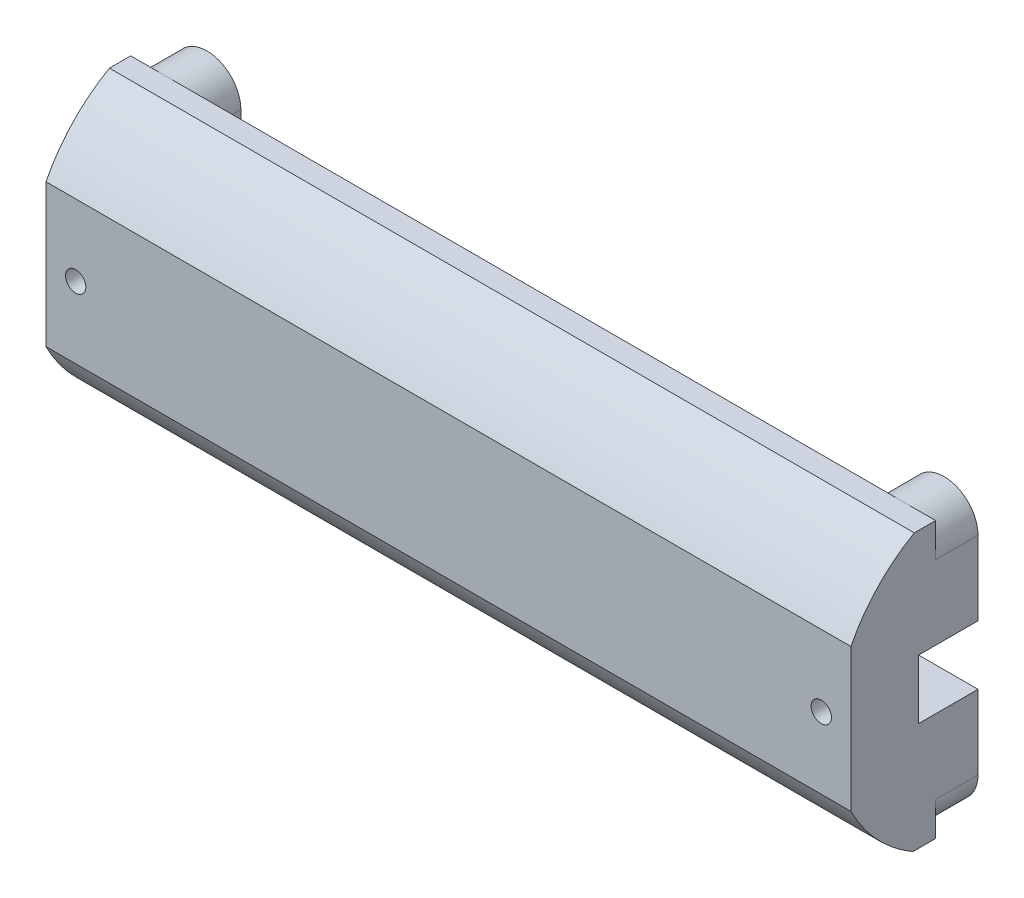
SolidWorks part; units mm, degrees
ref_plane "Front Plane" through (0, 0, 0) normal (0, 0, 1) x (1, 0, 0)
ref_plane "Top Plane" through (0, 0, 0) normal (0, 1, 0) x (1, 0, 0)
ref_plane "Right Plane" through (0, 0, 0) normal (1, 0, 0) x (0, 0, -1)
sketch "Sketch1" plane through (0, 0, 0) normal (0, 0, 1) x (1, 0, 0)
  circle A5 centre (-43.5, -12.25) radius 4
  circle A6 centre (-43.5, -12.25) radius 4
  circle A8 centre (-43.5, 12.25) radius 4
  circle A9 centre (-43.5, 12.25) radius 4
  circle A11 centre (43.5, -12.25) radius 4
  circle A12 centre (43.5, -12.25) radius 4
  circle A14 centre (43.5, 12.25) radius 4
  circle A15 centre (43.5, 12.25) radius 4
  circle A17 centre (-43.5, -12.25) radius 1.5
  circle A18 centre (-43.5, -12.25) radius 1.5
  circle A20 centre (-43.5, 12.25) radius 1.5
  circle A21 centre (-43.5, 12.25) radius 1.5
  circle A23 centre (43.5, -12.25) radius 1.5
  circle A24 centre (43.5, -12.25) radius 1.5
  circle A26 centre (43.5, 12.25) radius 1.5
  circle A27 centre (43.5, 12.25) radius 1.5
  dimension "D1" = 2.5
  dimension "D2" = 2.5
  dimension "D3" = 2.5
  dimension "D4" = 2.5
  dimension "D5" = 0
  dimension "D6" = 0
  dimension "D7" = 0
  dimension "D8" = 0
extrude "Boss-Extrude1" add sketch "Sketch1" along normal blind 5
sketch "Sketch2" plane through (0, 0, 5) normal (0, 0, 1) x (1, 0, 0)
  line L0 (-43.5, 12.25) -> (-43.5, 16.25)
  line L1 (-43.5, 16.25) -> (-47.5, 16.25)
  line L2 (43.5, -12.25) -> (47.5, -12.25)
  line L3 (47.5, -12.25) -> (47.5, -16.25)
  line L5 (-47.5, 16.25) -> (47.5, 16.25)
  line L6 (-47.5, 16.25) -> (-47.5, -16.25)
  line L7 (-47.5, -16.25) -> (47.5, -16.25)
  line L8 (47.5, 16.25) -> (47.5, -16.25)
  circle A2 centre (43.5, 12.25) radius 4
  circle A3 centre (43.5, 12.25) radius 4
  circle A4 centre (43.5, 12.25) radius 4
  circle A5 centre (-43.5, 12.25) radius 4
  circle A6 centre (-43.5, 12.25) radius 4
  circle A9 centre (43.5, -12.25) radius 4
  circle A10 centre (43.5, -12.25) radius 4
  dimension "D1" = 0
  dimension "D2" = 0
  dimension "D3" = 0
  dimension "D4" = 0
extrude "Boss-Extrude2" add sketch "Sketch2" along normal blind 10
sketch "Sketch3" plane through (0, 0, 5) normal (0, 0, -1) x (-1, 0, 0)
  line L0 (0, 16.25) -> (0, -16.25)
  line L1 (43.5, 16.25) -> (-43.5, 16.25) construction
  line L2 (43.5, -16.25) -> (-43.5, -16.25) construction
  line L3 (0, 0) -> (0, 7.1)
  line L4 (0, 7.1) -> (22.5, 7.1)
  line L5 (0, 0) -> (-6.8637, 0)
  line L6 (-22.5, -7.1) -> (22.5, -7.1)
  line L8 (-22.5, -7.1) -> (22.5, -7.1)
  line L9 (-22.5, -7.1) -> (-22.5, 7.1)
  line L10 (-22.5, 7.1) -> (22.5, 7.1)
  line L11 (22.5, -7.1) -> (22.5, 7.1)
  point P13 (0, -7.1)
extrude "Cut-Extrude1" cut sketch "Sketch3" against normal blind 9
sketch "Sketch4" plane through (0, 0, 5) normal (0, 0, -1) x (-1, 0, 0)
  line L2 (-22.5, 7.1) -> (-27.5, 7.1)
  line L3 (22.5, -7.1) -> (27.5, -7.1)
  line L5 (27.5, -7.1) -> (-27.5, -7.1)
  line L6 (27.5, -7.1) -> (27.5, 7.1)
  line L7 (27.5, 7.1) -> (-27.5, 7.1)
  line L8 (-27.5, -7.1) -> (-27.5, 7.1)
extrude "Cut-Extrude2" cut sketch "Sketch4" against normal blind 4 contours L8 L5 L2 M16 | M13 M16 M15 M14 | L6 L7 L3 M14
sketch "Sketch5" plane through (0, 0, 9) normal (0, 0, -1) x (-1, 0, 0)
  circle A2 centre (-24.8, -0.2) radius 1.4
  circle A3 centre (-24.8, -0.2) radius 1.4
  circle A5 centre (24.8, -0.2) radius 1.6
  circle A6 centre (24.8, -0.2) radius 1.6
  dimension "D1" = 0.1
  dimension "D2" = 0.1
extrude "Cut-Extrude3" cut sketch "Sketch5" against normal blind 5
sketch "Sketch6" plane through (0, 0, 5) normal (0, 0, -1) x (-1, 0, 0)
  line L4 (-47.5, 12.25) -> (-47.5, -12.25)
  line L5 (47.5, -12.25) -> (47.5, 12.25)
  line L6 (-39.5, 12.25) -> (-39.5, -12.25)
  line L7 (39.5, 12.25) -> (39.5, -12.25)
  line L8 (-47.5, 12.25) -> (-47.5, -12.25)
  line L9 (-43.5, -16.25) -> (43.5, -16.25)
  line L10 (47.5, -12.25) -> (47.5, 12.25)
  line L11 (43.5, 16.25) -> (-43.5, 16.25)
  line L12 (-47.5, 12.25) -> (-47.5, -12.25)
  line L13 (-43.5, -16.25) -> (43.5, -16.25)
  line L14 (47.5, -12.25) -> (47.5, 12.25)
  line L15 (43.5, 16.25) -> (-43.5, 16.25)
  arc A4 (-47.5, 12.25) -> (-43.5, 16.25) centre (-43.5, 12.25) ccw
  arc A5 (-43.5, -16.25) -> (-47.5, -12.25) centre (-43.5, -12.25) ccw
  arc A6 (47.5, -12.25) -> (43.5, -16.25) centre (43.5, -12.25) ccw
  arc A7 (43.5, 16.25) -> (47.5, 12.25) centre (43.5, 12.25) ccw
  arc A8 (-47.5, 12.25) -> (-43.5, 16.25) centre (-43.5, 12.25) ccw
  arc A9 (-43.5, -16.25) -> (-47.5, -12.25) centre (-43.5, -12.25) ccw
  arc A10 (47.5, -12.25) -> (43.5, -16.25) centre (43.5, -12.25) ccw
  arc A11 (43.5, 16.25) -> (47.5, 12.25) centre (43.5, 12.25) ccw
  arc A12 (-47.5, 12.25) -> (-43.5, 16.25) centre (-43.5, 12.25) ccw
  arc A13 (-43.5, -16.25) -> (-47.5, -12.25) centre (-43.5, -12.25) ccw
  arc A14 (47.5, -12.25) -> (43.5, -16.25) centre (43.5, -12.25) ccw
  arc A15 (43.5, 16.25) -> (47.5, 12.25) centre (43.5, 12.25) ccw
  dimension "D1" = 0
  dimension "D2" = 0
extrude "Boss-Extrude3" add sketch "Sketch6" along normal up to surface (5 mm away) contours L7 M15 M13 M14 | L6 M9 M10 M11 up to face at (47.5, -12.25, 0)
sketch "Sketch8" plane through (47.5, 0, 0) normal (1, 0, 0) x (0, 0, -1)
  line L4 (18.4999, -8.4753) -> (18.4999, 8.377)
  line L5 (-15, 8.377) -> (-15, -8.4753)
  line L6 (18.4999, -8.4753) -> (18.4999, 8.377)
  line L7 (-15, 8.377) -> (-15, -8.4753)
  line L17 (-5, -16.25) -> (-15, -16.25)
  line L18 (-15, -16.25) -> (-15, 16.25)
  line L19 (-15, 16.25) -> (-5, 16.25)
  line L20 (-5, -16.25) -> (-15, -16.25)
  line L21 (-15, -16.25) -> (-15, 16.25)
  line L22 (-15, 16.25) -> (-5, 16.25)
  arc A6 (18.4999, 8.377) -> (-15, 8.377) centre (1.75, -0.0491) ccw
  arc A7 (-15, -8.4753) -> (18.4999, -8.4753) centre (1.75, -0.0491) ccw
  arc A8 (18.4999, 8.377) -> (-15, 8.377) centre (1.75, -0.0491) ccw
  arc A9 (-15, -8.4753) -> (18.4999, -8.4753) centre (1.75, -0.0491) ccw
  dimension "D1" = 2.2
  dimension "D2" = 0
extrude "Cut-Extrude5" cut sketch "Sketch8" against normal through all contours A8 L22 M10 | A9 M10 M11
sketch "Sketch9" plane through (-47.5, 0, 0) normal (-1, 0, 0) x (0, 0, 1)
  line L3 (0, 12.25) -> (0, -12.25) construction
  line L5 (7, 3.5) -> (0, 3.5)
  line L6 (7, 3.5) -> (7, -3.5)
  line L7 (7, -3.5) -> (0, -3.5)
  line L8 (0, 3.5) -> (0, -3.5)
extrude "Cut-Extrude6" cut sketch "Sketch9" against normal through all
sketch "Sketch10" plane through (0, 0, 15) normal (0, 0, 1) x (1, 0, 0)
  line L0 (47.5, -0.0491) -> (44, -0.0491)
  line L1 (47.5, 8.377) -> (47.5, -8.4753) construction
  line L2 (-47.5, -0.0491) -> (-44, -0.0491)
  line L3 (-47.5, 8.377) -> (-47.5, -8.4753) construction
  circle A0 centre (-44, -0.0491) radius 1.2
  circle A1 centre (44, -0.0491) radius 1.2
extrude "Cut-Extrude7" cut sketch "Sketch10" against normal through all
